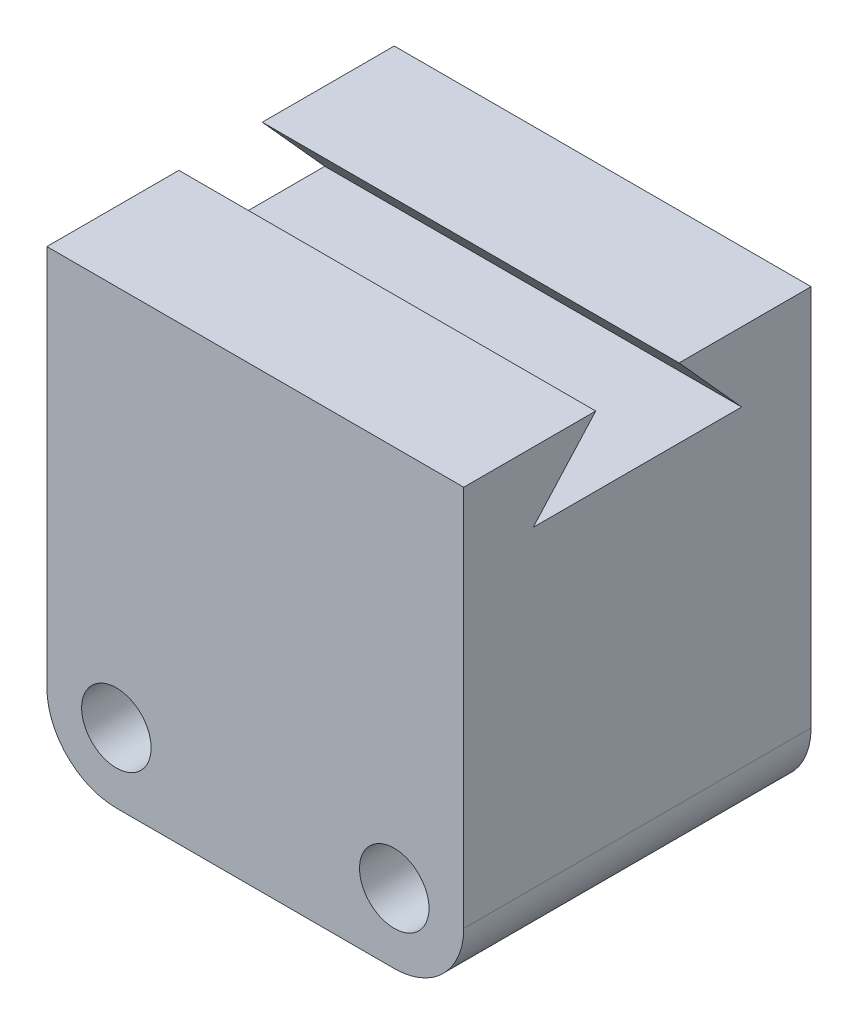
SolidWorks part; units mm, degrees
ref_plane "Front Plane" through (0, 0, 0) normal (0, 0, 1) x (1, 0, 0)
ref_plane "Top Plane" through (0, 0, 0) normal (0, 1, 0) x (1, 0, 0)
ref_plane "Right Plane" through (0, 0, 0) normal (1, 0, 0) x (0, 0, -1)
sketch "Sketch1" plane through (0, 0, 0) normal (0, 0, 1) x (1, 0, 0)
  line L1 (-33.5783, 15.2997) -> (26.4217, 15.2997)
  line L2 (-33.5783, 15.2997) -> (-33.5783, -49.7003)
  line L3 (-33.5783, -49.7003) -> (26.4217, -49.7003)
  line L4 (26.4217, 15.2997) -> (26.4217, -49.7003)
  dimension "D1" = 65
  dimension "D2" = 60
extrude "Boss-Extrude1" add sketch "Sketch1" along normal mid plane 50
sketch "Sketch3" plane through (26.4217, 0, 0) normal (1, 0, 0) x (0, 0, -1)
  line L0 (-15, 5.2997) -> (15, 5.2997)
  line L1 (-25, 15.2997) -> (25, 15.2997) construction
  line L2 (-15, 5.2997) -> (-6, 15.2997)
  line L3 (-6, 15.2997) -> (6, 15.2997)
  line L4 (0, 15.2997) -> (0, 8.3085) construction
  line L5 (15, 5.2997) -> (6, 15.2997)
  point P4 (0, 5.2997)
  dimension "D1" = 30
  dimension "D2" = 10
  dimension "D3" = 6
extrude "Cut-Extrude1" cut sketch "Sketch3" against normal up to surface (60 mm away) up to face at (-33.5783, -17.2003, 0)
sketch "Sketch4" plane through (0, 0, 25) normal (0, 0, 1) x (1, 0, 0)
  line L0 (26.4217, -49.7003) -> (26.4217, 15.2997) construction
  line L1 (-33.5783, -49.7003) -> (26.4217, -49.7003) construction
  circle A0 centre (16.4217, -39.7003) radius 5
  circle A1 centre (-23.5783, -39.7003) radius 5
  dimension "D2" = 10
  dimension "D1" = 40
  dimension "D3" = 10
  dimension "D4" = 10
extrude "Cut-Extrude2" cut sketch "Sketch4" against normal through all
fillet "Fillet1" radius 10 2 edges at (-33.5783, -49.7003, 0) (26.4217, -49.7003, 0)
scale "Scale1" bodies to scale 103 scale about centroid uniform scaling yes scale factor 0.3
